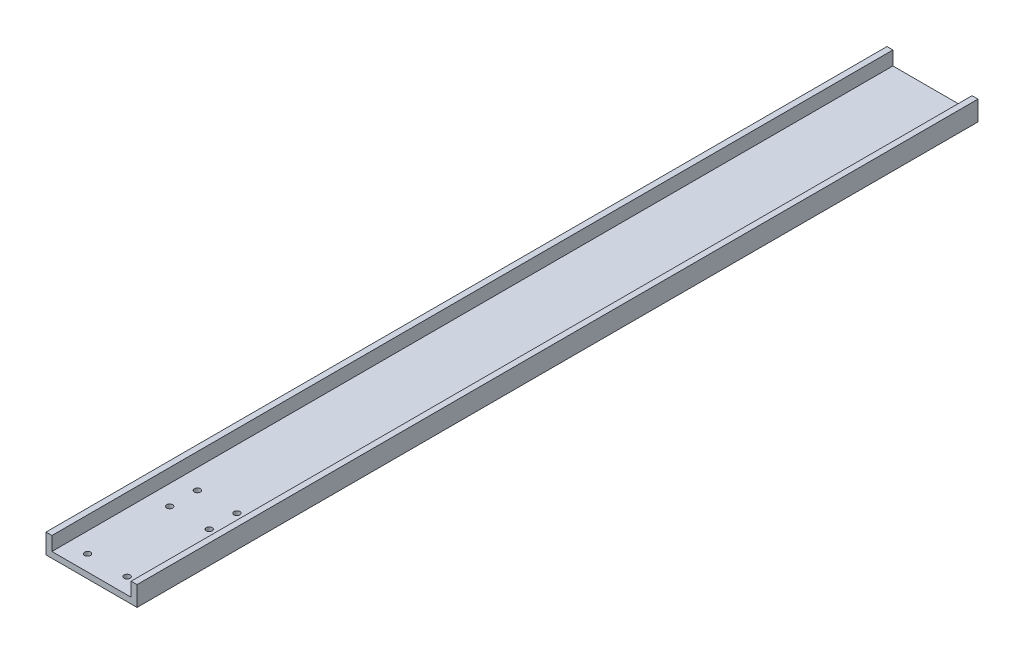
SolidWorks part; units mm, degrees
ref_plane "Front Plane" through (0, 0, 0) normal (0, 0, 1) x (1, 0, 0)
ref_plane "Top Plane" through (0, 0, 0) normal (0, 1, 0) x (1, 0, 0)
ref_plane "Right Plane" through (0, 0, 0) normal (1, 0, 0) x (0, 0, -1)
sketch "Sketch1" plane through (0, 0, 0) normal (0, 0, 1) x (1, 0, 0)
  line L0 (0, 0) -> (0, 7)
  line L1 (0, 7) -> (-3, 7)
  line L2 (-3, 7) -> (-3, -3)
  line L3 (-3, -3) -> (43, -3)
  line L4 (43, -3) -> (43, 7)
  line L5 (43, 7) -> (40, 7)
  line L6 (40, 7) -> (40, 0)
  line L7 (40, 0) -> (0, 0)
  dimension "D1" = 3
  dimension "D2" = 3
  dimension "D3" = 3
  dimension "D4" = 10
  dimension "D5" = 40
extrude "Boss-Extrude1" add sketch "Sketch1" along normal blind 425 contours L7 L0 L1 L2 L3 L4 L5 L6
hole_wizard "Ø3.0mm Dowel Hole1" positions "Sketch3" profile "Sketch2" hole size "Ø3.0" standard "ISO"
sketch "Sketch3" plane through (0, 0, 0) normal (0, 1, 0) x (1, 0, 0)
  line L0 (-3, -425) -> (-3, 0) construction
  line L1 (40, -425) -> (0, -425) construction
  point P0 (10, -375.5)
  point P2 (30, -375.5)
  point P4 (30, -361.5)
  point P6 (10, -361.5)
  dimension "D1" = 20
  dimension "D2" = 14
  dimension "D3" = 13
  dimension "D4" = 49.5
sketch "Sketch2" plane through (10, 0, 375.5) normal (1, 0, 0) x (0, 0, 1)
  line L0 (0, 0) -> (0, 15.9013)
  line L1 (0, 15.9013) -> (1.5, 15)
  line L2 (1.5, 15) -> (1.5, 0)
  line L5 (1.5, 0) -> (0, 0)
  line L10 (0, 15.9013) -> (-1.5, 15) construction
  line L11 (0, -6.35) -> (0, 107.95) construction
  dimension "Hole Dia." = 3
  dimension "Hole Depth" = 15
  dimension "Drill Angle" = 118
hole_wizard "Ø3.0mm Dowel Hole2" positions "Sketch5" profile "Sketch4" hole size "Ø3.0" standard "ISO"
sketch "Sketch5" plane through (0, -3, 0) normal (0, -1, 0) x (-1, 0, 0)
  line L0 (3, -425) -> (3, 0) construction
  line L1 (3, -425) -> (-43, -425) construction
  point P0 (-30, -417)
  point P2 (-10, -417)
  dimension "D1" = 20
  dimension "D2" = 13
  dimension "D3" = 8
sketch "Sketch4" plane through (30, -3, 417) normal (1, 0, 0) x (0, 0, -1)
  line L0 (0, 0) -> (0, 15.9013)
  line L1 (0, 15.9013) -> (1.5, 15)
  line L2 (1.5, 15) -> (1.5, 0)
  line L5 (1.5, 0) -> (0, 0)
  line L10 (0, 15.9013) -> (-1.5, 15) construction
  line L11 (0, -6.35) -> (0, 107.95) construction
  dimension "Hole Dia." = 3
  dimension "Hole Depth" = 15
  dimension "Drill Angle" = 118
